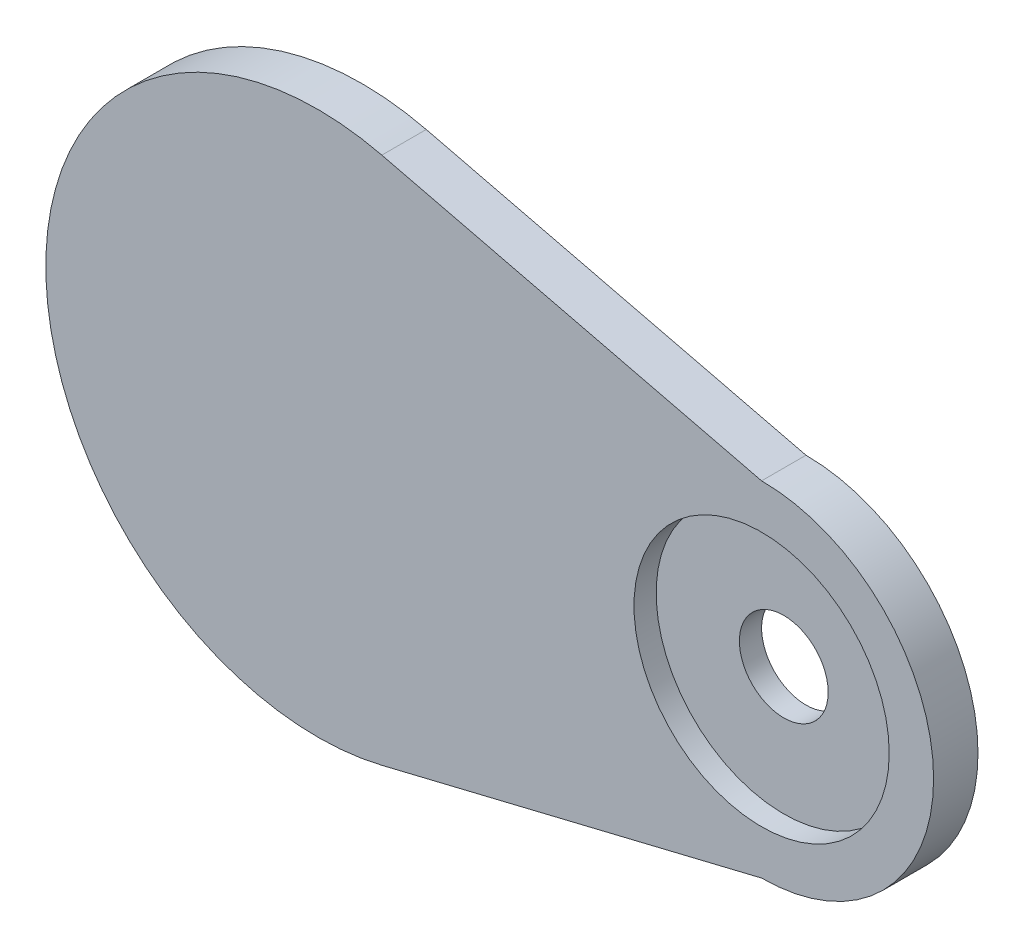
SolidWorks part; units mm, degrees
ref_plane "前视基准面" through (0, 0, 0) normal (0, 0, 1) x (1, 0, 0)
ref_plane "上视基准面" through (0, 0, 0) normal (0, 1, 0) x (1, 0, 0)
ref_plane "右视基准面" through (0, 0, 0) normal (1, 0, 0) x (0, 0, -1)
sketch "草图1" plane through (0, 0, 0) normal (0, 0, 1) x (1, 0, 0)
  line L0 (13.4906, 0.8667) -> (1.9906, 0.8667)
  line L1 (13.4906, 16.3667) -> (-20.7288, 24.675)
  line L2 (13.4906, -14.6333) -> (-20.7288, -22.9416)
  circle A0 centre (13.4906, 0.8667) radius 11.5 construction
  arc A1 (13.4906, -14.6333) -> (13.4906, 16.3667) centre (13.4906, 0.8667) ccw
  arc A2 (-20.7288, 24.675) -> (-20.7288, -22.9416) centre (-26.5094, 0.8667) ccw
  circle A3 centre (13.4906, 0.8667) radius 15.5 construction
  dimension "D1" = 23
  dimension "D3" = 40
  dimension "D2" = 4
extrude "凸台-拉伸1" add sketch "草图1" along normal blind 4
sketch "草图2" plane through (0, 0, 4) normal (0, 0, 1) x (1, 0, 0)
  circle A0 centre (13.4906, 0.8667) radius 11.5
extrude "切除-拉伸1" cut sketch "草图2" against normal blind 2
sketch "草图3" plane through (0, 0, 2) normal (0, 0, 1) x (1, 0, 0)
  circle A0 centre (13.4906, 0.8667) radius 4
  dimension "D1" = 8
extrude "切除-拉伸2" cut sketch "草图3" against normal blind 2
